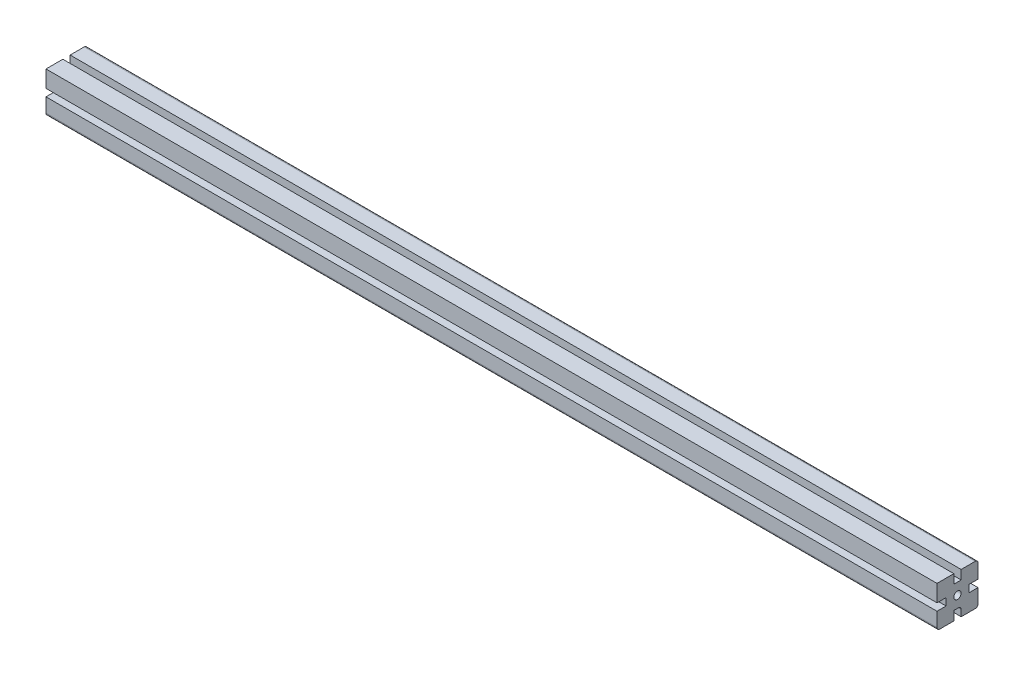
SolidWorks part; units mm, degrees
ref_plane "Plan de face" through (0, 0, 0) normal (0, 0, 1) x (1, 0, 0)
ref_plane "Plan de dessus" through (0, 0, 0) normal (0, 1, 0) x (1, 0, 0)
ref_plane "Plan de droite" through (0, 0, 0) normal (1, 0, 0) x (0, 0, -1)
ref_plane "Plan1" through (1000, 0, 0) normal (1, 0, 0) x (0, 0, -1)
sketch "Esquisse1" plane through (1000, 0, 0) normal (1, 0, 0) x (0, 0, -1)
  line L0 (22.5, -4) -> (12.5, -4)
  line L1 (12.5, -4) -> (12.5, 4)
  line L2 (12.5, 4) -> (22.5, 4)
  line L3 (22.5, 4) -> (22.5, 22.5)
  line L4 (22.5, 22.5) -> (4, 22.5)
  line L5 (4, 22.5) -> (4, 12.5)
  line L6 (4, 12.5) -> (-4, 12.5)
  line L7 (-4, 12.5) -> (-4, 22.5)
  line L8 (-4, 22.5) -> (-22.5, 22.5)
  line L9 (-22.5, 22.5) -> (-22.5, 4)
  line L10 (-22.5, 4) -> (-12.5, 4)
  line L11 (-12.5, 4) -> (-12.5, -4)
  line L12 (-12.5, -4) -> (-22.5, -4)
  line L13 (-22.5, -4) -> (-22.5, -22.5)
  line L14 (-22.5, -22.5) -> (-4, -22.5)
  line L15 (-4, -22.5) -> (-4, -12.5)
  line L16 (-4, -12.5) -> (4, -12.5)
  line L17 (4, -12.5) -> (4, -22.5)
  line L18 (4, -22.5) -> (22.5, -22.5)
  line L19 (22.5, -22.5) -> (22.5, -4)
  line L20 (0, 0) -> (22.5, 0) construction
  line L21 (0, 0) -> (0, 22.5) construction
  circle A0 centre (0, 0) radius 4
  dimension "D1" = 4
  dimension "D2" = 45
  dimension "D3" = 45
  dimension "D4" = 4
  dimension "D5" = 10
  dimension "D6" = 10
  dimension "D7" = 10
  dimension "D8" = 10
  dimension "D9" = 22.5
extrude "Boss.-Extru.1" add sketch "Esquisse1" against normal blind 978
fillet "Congé1" radius 3 4 edges at (511, -22.5, -22.5) (511, -22.5, 22.5) (511, 22.5, -22.5) (511, -12.5, -4)
